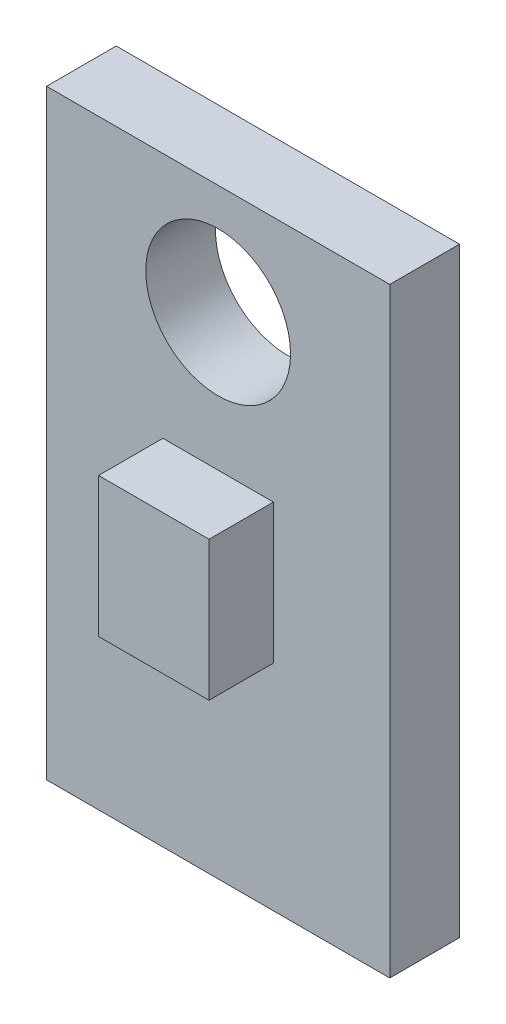
SolidWorks part; units mm, degrees
ref_plane "Front Plane" through (0, 0, 0) normal (0, 0, 1) x (1, 0, 0)
ref_plane "Top Plane" through (0, 0, 0) normal (0, 1, 0) x (1, 0, 0)
ref_plane "Right Plane" through (0, 0, 0) normal (1, 0, 0) x (0, 0, -1)
sketch "Sketch1" plane through (0, 0, 0) normal (0, 0, 1) x (1, 0, 0)
  line L1 (0, 0) -> (8.128, 0)
  line L2 (0, 0) -> (0, 14.224)
  line L3 (0, 14.224) -> (8.128, 14.224)
  line L4 (8.128, 0) -> (8.128, 14.224)
  dimension "D1" = 14.224
  dimension "D2" = 8.128
extrude "Boss-Extrude1" add sketch "Sketch1" along normal blind 1.651
sketch "Sketch2" plane through (0, 0, 1.651) normal (0, 0, 1) x (1, 0, 0)
  line L0 (0, 0) -> (8.128, 0) construction
  line L1 (5.3721, 5.08) -> (2.7559, 5.08)
  line L2 (5.3721, 5.08) -> (5.3721, 8.382)
  line L3 (5.3721, 8.382) -> (2.7559, 8.382)
  line L4 (2.7559, 5.08) -> (2.7559, 8.382)
  point P6 (4.064, 8.382)
  point P7 (4.064, 0)
  dimension "D1" = 3.302
  dimension "D2" = 2.6162
  dimension "D3" = 8.382
extrude "Boss-Extrude2" add sketch "Sketch2" along normal blind 1.524
sketch "Sketch3" plane through (0, 0, 1.651) normal (0, 0, 1) x (1, 0, 0)
  line L1 (8.128, 14.224) -> (0, 14.224) construction
  circle A0 centre (4.064, 11.6205) radius 1.7145
  point P2 (4.064, 14.224)
  point P3 (4.064, 13.335)
  dimension "D1" = 3.429
  dimension "D2" = 0.889
extrude "Cut-Extrude1" cut sketch "Sketch3" against normal through all
